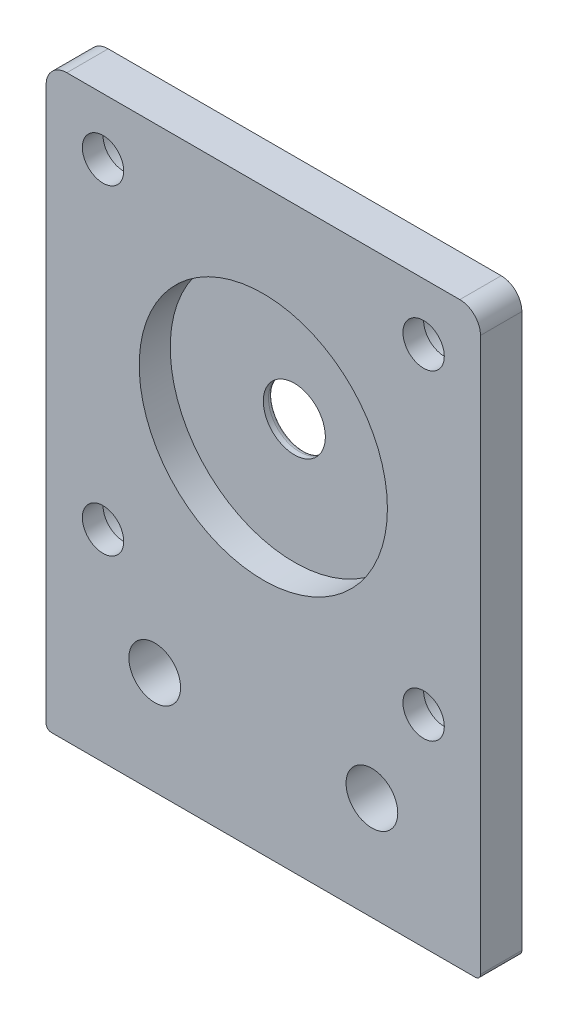
SolidWorks part; units mm, degrees
ref_plane "Front Plane" through (0, 0, 0) normal (0, 0, 1) x (1, 0, 0)
ref_plane "Top Plane" through (0, 0, 0) normal (0, 1, 0) x (1, 0, 0)
ref_plane "Right Plane" through (0, 0, 0) normal (1, 0, 0) x (0, 0, -1)
sketch "Sketch1" plane through (0, 0, 0) normal (0, 0, 1) x (1, 0, 0)
  line L1 (0, 0) -> (42, 0)
  line L2 (0, 0) -> (0, 56)
  line L4 (42, 0) -> (42, 51.3716)
  line L5 (0, 51.3716) -> (0, 18.6284) construction
  line L9 (4.6284, 56) -> (37.3716, 56)
  line L10 (4.6284, 56) -> (0, 56)
  line L11 (37.3716, 56) -> (42, 56)
  line L12 (42, 56) -> (42, 51.3716)
  arc A0 (38.7858, 55.4142) -> (37.3716, 56) centre (37.3716, 54) ccw construction
  circle A1 centre (21, 35) radius 3
extrude "Boss-Extrude1" add sketch "Sketch1" along normal blind 4
sketch "Sketch5" plane through (0, 0, 4) normal (0, 0, 1) x (1, 0, 0)
  circle A0 centre (21, 35) radius 12
extrude "Cut-Extrude1" cut sketch "Sketch5" against normal blind 3
fillet "Fillet1" radius 2 2 edges at (42, 56, 2) (0, 56, 2)
fillet "Fillet2" radius 0.5 2 edges at (42, 0, 2) (0, 0, 2)
fillet "Fillet3" radius 0.5 1 edges at (24, 35, 0)
sketch "Sketch6" plane through (0, 0, 4) normal (0, 0, 1) x (1, 0, 0)
  circle A0 centre (10.5, 10) radius 2.5
  circle A1 centre (31.5, 10) radius 2.5
extrude "Cut-Extrude2" cut sketch "Sketch6" against normal blind 10
sketch "Sketch7" plane through (0, 0, 4) normal (0, 0, 1) x (1, 0, 0)
  circle A0 centre (5.5, 50.5) radius 2
  circle A1 centre (5.5, 19.5) radius 2
  circle A2 centre (36.5, 19.5) radius 2
  circle A3 centre (36.5, 50.5) radius 2
extrude "Cut-Extrude3" cut sketch "Sketch7" against normal blind 10
sketch "Sketch8" plane through (0, 0, 0) normal (0, 0, -1) x (-1, 0, 0)
  circle A0 centre (-36.5, 50.5) radius 3.5
  circle A1 centre (-36.5, 19.5) radius 3.5
  circle A2 centre (-5.5, 19.5) radius 3.5
  circle A3 centre (-5.5, 50.5) radius 3.5
extrude "Cut-Extrude4" cut sketch "Sketch8" against normal blind 2
